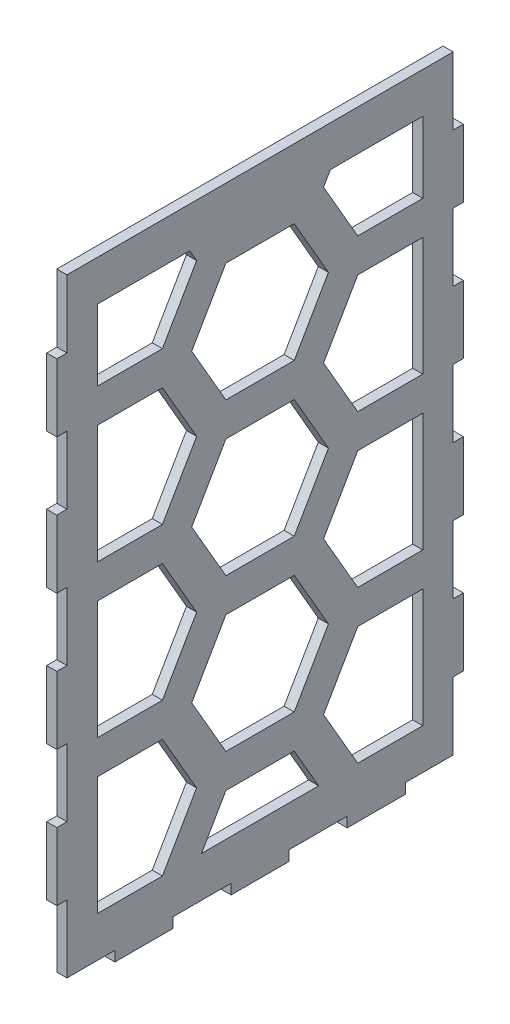
SolidWorks part; units mm, degrees
ref_plane "Front Plane" through (0, 0, 0) normal (0, 0, 1) x (1, 0, 0)
ref_plane "Top Plane" through (0, 0, 0) normal (0, 1, 0) x (1, 0, 0)
ref_plane "Right Plane" through (0, 0, 0) normal (1, 0, 0) x (0, 0, -1)
sketch "Sketch1" plane through (0, 0, 0) normal (1, 0, 0) x (0, 0, -1)
  line L1 (-57.0864, -90) -> (57.0864, -90)
  line L2 (-57.0864, -90) -> (-57.0864, 90)
  line L3 (-57.0864, 90) -> (57.0864, 90)
  line L4 (57.0864, -90) -> (57.0864, 90)
  line L5 (-57.0864, -90) -> (57.0864, 90) construction
  line L6 (-57.0864, 90) -> (57.0864, -90) construction
  point P0 (0, 0)
  dimension "D1" = 114.1727
  dimension "D2" = 180
extrude "Boss-Extrude1" add sketch "Sketch1" along normal blind 3
sketch "Sketch2" plane through (3, 0, 0) normal (1, 0, 0) x (0, 0, -1)
  line L0 (-57.0864, -90) -> (57.0864, -90) construction
  line L1 (-42.9188, -93) -> (-25.7513, -93)
  line L2 (-42.9188, -93) -> (-42.9188, -90)
  line L3 (-42.9188, -90) -> (-25.7513, -90)
  line L4 (-25.7513, -93) -> (-25.7513, -90)
  line L5 (-42.9188, -93) -> (-25.7513, -90) construction
  line L6 (-42.9188, -90) -> (-25.7513, -93) construction
  line L7 (-60.0864, -93) -> (-42.9188, -93) construction
  line L8 (-8.5838, -93) -> (8.5838, -93)
  line L9 (-8.5838, -93) -> (-8.5838, -90)
  line L10 (-8.5838, -90) -> (8.5838, -90)
  line L11 (8.5838, -93) -> (8.5838, -90)
  line L12 (-8.5838, -93) -> (8.5838, -90) construction
  line L13 (-8.5838, -90) -> (8.5838, -93) construction
  line L14 (25.7513, -93) -> (42.9188, -93)
  line L15 (25.7513, -93) -> (25.7513, -90)
  line L16 (25.7513, -90) -> (42.9188, -90)
  line L17 (42.9188, -93) -> (42.9188, -90)
  line L18 (25.7513, -93) -> (42.9188, -90) construction
  line L19 (25.7513, -90) -> (42.9188, -93) construction
  line L20 (-25.7513, -93) -> (-8.5838, -93) construction
  line L21 (8.5838, -93) -> (25.7513, -93) construction
  line L22 (42.9188, -93) -> (60.0864, -93) construction
  line L23 (-57.0864, 90) -> (-57.0864, -90) construction
  line L24 (57.0864, -90) -> (57.0864, 90) construction
  line L25 (60.0863, -70) -> (57.0864, -70)
  line L26 (60.0863, -70) -> (60.0864, -50)
  line L27 (60.0864, -50) -> (57.0864, -50)
  line L28 (57.0864, -70) -> (57.0864, -50)
  line L29 (60.0863, -70) -> (57.0864, -50) construction
  line L30 (60.0864, -50) -> (57.0864, -70) construction
  line L31 (60.0863, 90) -> (60.0863, 70) construction
  line L32 (60.0863, -30) -> (57.0864, -30)
  line L33 (60.0863, -30) -> (60.0863, -10)
  line L34 (60.0863, -10) -> (57.0864, -10)
  line L35 (57.0864, -30) -> (57.0864, -10)
  line L36 (60.0863, -30) -> (57.0864, -10) construction
  line L37 (60.0863, -10) -> (57.0864, -30) construction
  line L38 (60.0863, 10) -> (57.0864, 10)
  line L39 (60.0863, 10) -> (60.0863, 30)
  line L40 (60.0863, 30) -> (57.0864, 30)
  line L41 (57.0864, 10) -> (57.0864, 30)
  line L42 (60.0863, 10) -> (57.0864, 30) construction
  line L43 (60.0863, 30) -> (57.0864, 10) construction
  line L44 (60.0863, 50) -> (57.0864, 50)
  line L45 (60.0863, 50) -> (60.0863, 70)
  line L46 (60.0863, 70) -> (57.0864, 70)
  line L47 (57.0864, 50) -> (57.0864, 70)
  line L48 (60.0863, 50) -> (57.0864, 70) construction
  line L49 (60.0863, 70) -> (57.0864, 50) construction
  line L50 (60.0863, 50) -> (60.0863, 30) construction
  line L51 (60.0863, 10) -> (60.0863, -10) construction
  line L52 (60.0863, -30) -> (60.0864, -50) construction
  line L53 (60.0863, -70) -> (60.0863, -90) construction
  line L54 (57.0864, 90) -> (-57.0864, 90) construction
  line L55 (0, -895.4773) -> (0, 49104.5227) construction
  line L56 (-60.0864, -50) -> (-57.0864, -50)
  line L57 (-57.0864, -70) -> (-57.0864, -50)
  line L58 (-60.0863, -70) -> (-57.0864, -70)
  line L59 (-60.0863, -70) -> (-60.0864, -50)
  line L60 (-60.0863, -10) -> (-57.0864, -10)
  line L61 (-57.0864, -30) -> (-57.0864, -10)
  line L62 (-60.0863, -30) -> (-57.0864, -30)
  line L63 (-60.0863, -30) -> (-60.0863, -10)
  line L64 (-60.0863, 30) -> (-57.0864, 30)
  line L65 (-57.0864, 10) -> (-57.0864, 30)
  line L66 (-60.0863, 10) -> (-57.0864, 10)
  line L67 (-60.0863, 10) -> (-60.0863, 30)
  line L68 (-60.0863, 70) -> (-57.0864, 70)
  line L69 (-57.0864, 50) -> (-57.0864, 70)
  line L70 (-60.0863, 50) -> (-57.0864, 50)
  line L71 (-60.0863, 50) -> (-60.0863, 70)
  point P0 (-34.3351, -91.5)
  point P7 (0, -91.5)
  point P12 (34.3351, -91.5)
  point P24 (58.5864, -60)
  point P29 (58.5864, -20)
  point P34 (58.5863, 20)
  point P39 (58.5864, 60)
  dimension "D1" = 3
  dimension "D2" = 3
extrude "Boss-Extrude2" add sketch "Sketch2" against normal up to surface (3 mm away) up to face at (0, 0, 0)
sketch "Sketch3" plane through (0, 0, -3) normal (-1, 0, 0) x (0, 0, 1)
  line L0 (-142.7809, -20.5) -> (-162.9882, -20.5)
  line L1 (-142.7809, -65.5) -> (-162.9882, -65.5)
  line L2 (-162.9882, -65.5) -> (-173.0918, -83)
  line L3 (-173.0918, -83) -> (-162.9882, -100.5)
  line L4 (-162.9882, -100.5) -> (-142.7809, -100.5)
  line L5 (-142.7809, -100.5) -> (-132.6773, -83)
  line L6 (-132.6773, -83) -> (-142.7809, -65.5)
  line L13 (-162.9882, -20.5) -> (-173.0918, -38)
  line L14 (-134.1207, -105.5) -> (-124.0171, -123)
  line L15 (-124.0171, -123) -> (-103.8098, -123)
  line L16 (-103.8098, -123) -> (-93.7062, -105.5)
  line L17 (-93.7062, -105.5) -> (-103.8098, -88)
  line L18 (-103.8098, -88) -> (-124.0171, -88)
  line L19 (-124.0171, -88) -> (-134.1207, -105.5)
  line L20 (-173.0918, -38) -> (-162.9882, -55.5)
  line L21 (-162.9882, -55.5) -> (-142.7809, -55.5)
  line L22 (-142.7809, -55.5) -> (-132.6773, -38)
  line L23 (-132.6773, -38) -> (-142.7809, -20.5)
  line L24 (-134.1207, -60.5) -> (-124.0171, -78)
  line L25 (-124.0171, -78) -> (-103.8098, -78)
  line L26 (-103.8098, -78) -> (-93.7062, -60.5)
  line L27 (-93.7062, -60.5) -> (-103.8098, -43)
  line L28 (-103.8098, -43) -> (-124.0171, -43)
  line L29 (-124.0171, -43) -> (-134.1207, -60.5)
  line L30 (-142.7809, 24.5) -> (-162.9882, 24.5)
  line L31 (-162.9882, 24.5) -> (-173.0918, 7)
  line L32 (-173.0918, 7) -> (-162.9882, -10.5)
  line L33 (-162.9882, -10.5) -> (-142.7809, -10.5)
  line L34 (-142.7809, -10.5) -> (-132.6773, 7)
  line L35 (-132.6773, 7) -> (-142.7809, 24.5)
  line L36 (-134.1207, -15.5) -> (-124.0171, -33)
  line L37 (-124.0171, -33) -> (-103.8098, -33)
  line L38 (-103.8098, -33) -> (-93.7062, -15.5)
  line L39 (-93.7062, -15.5) -> (-103.8098, 2)
  line L40 (-103.8098, 2) -> (-124.0171, 2)
  line L41 (-124.0171, 2) -> (-134.1207, -15.5)
  line L42 (-142.7809, 69.5) -> (-162.9882, 69.5)
  line L43 (-162.9882, 69.5) -> (-173.0918, 52)
  line L44 (-173.0918, 52) -> (-162.9882, 34.5)
  line L45 (-162.9882, 34.5) -> (-142.7809, 34.5)
  line L46 (-142.7809, 34.5) -> (-132.6773, 52)
  line L47 (-132.6773, 52) -> (-142.7809, 69.5)
  line L48 (-134.1207, 29.5) -> (-124.0171, 12)
  line L49 (-124.0171, 12) -> (-103.8098, 12)
  line L50 (-103.8098, 12) -> (-93.7062, 29.5)
  line L51 (-93.7062, 29.5) -> (-103.8098, 47)
  line L52 (-103.8098, 47) -> (-124.0171, 47)
  line L53 (-124.0171, 47) -> (-134.1207, 29.5)
  line L54 (-142.7809, 114.5) -> (-162.9882, 114.5)
  line L55 (-162.9882, 114.5) -> (-173.0918, 97)
  line L56 (-173.0918, 97) -> (-162.9882, 79.5)
  line L57 (-162.9882, 79.5) -> (-142.7809, 79.5)
  line L58 (-142.7809, 79.5) -> (-132.6773, 97)
  line L59 (-132.6773, 97) -> (-142.7809, 114.5)
  line L60 (-134.1207, 74.5) -> (-124.0171, 57)
  line L61 (-124.0171, 57) -> (-103.8098, 57)
  line L62 (-103.8098, 57) -> (-93.7062, 74.5)
  line L63 (-93.7062, 74.5) -> (-103.8098, 92)
  line L64 (-103.8098, 92) -> (-124.0171, 92)
  line L65 (-124.0171, 92) -> (-134.1207, 74.5)
  line L66 (-142.7809, 159.5) -> (-162.9882, 159.5)
  line L67 (-162.9882, 159.5) -> (-173.0918, 142)
  line L68 (-173.0918, 142) -> (-162.9882, 124.5)
  line L69 (-162.9882, 124.5) -> (-142.7809, 124.5)
  line L70 (-142.7809, 124.5) -> (-132.6773, 142)
  line L71 (-132.6773, 142) -> (-142.7809, 159.5)
  line L72 (-134.1207, 119.5) -> (-124.0171, 102)
  line L73 (-124.0171, 102) -> (-103.8098, 102)
  line L74 (-103.8098, 102) -> (-93.7062, 119.5)
  line L75 (-93.7062, 119.5) -> (-103.8098, 137)
  line L76 (-103.8098, 137) -> (-124.0171, 137)
  line L77 (-124.0171, 137) -> (-134.1207, 119.5)
  line L102 (-142.7809, -65.5) -> (-142.7809, -20.5) construction
  line L103 (-124.0171, -88) -> (-124.0171, -78) construction
  line L104 (-137.7291, -74.25) -> (-129.0689, -69.25) construction
  line L105 (-56.1784, 119.5) -> (-46.0748, 102)
  line L106 (-46.0748, 102) -> (-25.8675, 102)
  line L107 (-25.8675, 102) -> (-15.7639, 119.5)
  line L108 (-15.7639, 119.5) -> (-25.8675, 137)
  line L109 (-25.8675, 137) -> (-46.0748, 137)
  line L110 (-46.0748, 137) -> (-56.1784, 119.5)
  line L111 (-64.8387, 159.5) -> (-85.0459, 159.5)
  line L112 (-85.0459, 159.5) -> (-95.1495, 142)
  line L113 (-95.1495, 142) -> (-85.0459, 124.5)
  line L114 (-85.0459, 124.5) -> (-64.8387, 124.5)
  line L115 (-64.8387, 124.5) -> (-54.735, 142)
  line L116 (-54.735, 142) -> (-64.8387, 159.5)
  line L117 (-64.8387, 114.5) -> (-85.0459, 114.5)
  line L118 (-85.0459, 114.5) -> (-95.1495, 97)
  line L119 (-95.1495, 97) -> (-85.0459, 79.5)
  line L120 (-85.0459, 79.5) -> (-64.8387, 79.5)
  line L121 (-64.8387, 79.5) -> (-54.735, 97)
  line L122 (-54.735, 97) -> (-64.8387, 114.5)
  line L123 (-64.8387, 69.5) -> (-85.0459, 69.5)
  line L124 (-85.0459, 69.5) -> (-95.1495, 52)
  line L125 (-95.1495, 52) -> (-85.0459, 34.5)
  line L126 (-85.0459, 34.5) -> (-64.8387, 34.5)
  line L127 (-64.8387, 34.5) -> (-54.735, 52)
  line L128 (-54.735, 52) -> (-64.8387, 69.5)
  line L129 (-64.8387, 24.5) -> (-85.0459, 24.5)
  line L130 (-85.0459, 24.5) -> (-95.1495, 7)
  line L131 (-95.1495, 7) -> (-85.0459, -10.5)
  line L132 (-85.0459, -10.5) -> (-64.8387, -10.5)
  line L133 (-64.8387, -10.5) -> (-54.735, 7)
  line L134 (-54.735, 7) -> (-64.8387, 24.5)
  line L135 (-56.1784, -15.5) -> (-46.0748, -33)
  line L136 (-46.0748, -33) -> (-25.8675, -33)
  line L137 (-25.8675, -33) -> (-15.7639, -15.5)
  line L138 (-15.7639, -15.5) -> (-25.8675, 2)
  line L139 (-25.8675, 2) -> (-46.0748, 2)
  line L140 (-46.0748, 2) -> (-56.1784, -15.5)
  line L141 (-64.8387, -20.5) -> (-85.0459, -20.5)
  line L142 (-85.0459, -20.5) -> (-95.1495, -38)
  line L143 (-95.1495, -38) -> (-85.0459, -55.5)
  line L144 (-85.0459, -55.5) -> (-64.8387, -55.5)
  line L145 (-64.8387, -55.5) -> (-54.735, -38)
  line L146 (-54.735, -38) -> (-64.8387, -20.5)
  line L147 (-56.1784, -60.5) -> (-46.0748, -78)
  line L148 (-46.0748, -78) -> (-25.8675, -78)
  line L149 (-25.8675, -78) -> (-15.7639, -60.5)
  line L150 (-15.7639, -60.5) -> (-25.8675, -43)
  line L151 (-25.8675, -43) -> (-46.0748, -43)
  line L152 (-46.0748, -43) -> (-56.1784, -60.5)
  line L153 (-64.8387, -65.5) -> (-85.0459, -65.5)
  line L154 (-85.0459, -65.5) -> (-95.1495, -83)
  line L155 (-95.1495, -83) -> (-85.0459, -100.5)
  line L156 (-85.0459, -100.5) -> (-64.8387, -100.5)
  line L157 (-64.8387, -100.5) -> (-54.735, -83)
  line L158 (-54.735, -83) -> (-64.8387, -65.5)
  line L159 (-56.1784, -105.5) -> (-46.0748, -123)
  line L160 (-46.0748, -123) -> (-25.8675, -123)
  line L161 (-25.8675, -123) -> (-15.7639, -105.5)
  line L162 (-15.7639, -105.5) -> (-25.8675, -88)
  line L163 (-25.8675, -88) -> (-46.0748, -88)
  line L164 (-46.0748, -88) -> (-56.1784, -105.5)
  line L165 (-56.1784, 29.5) -> (-46.0748, 12)
  line L166 (-46.0748, 12) -> (-25.8675, 12)
  line L167 (-25.8675, 12) -> (-15.7639, 29.5)
  line L168 (-15.7639, 29.5) -> (-25.8675, 47)
  line L169 (-25.8675, 47) -> (-46.0748, 47)
  line L170 (-46.0748, 47) -> (-56.1784, 29.5)
  line L171 (-56.1784, 74.5) -> (-46.0748, 57)
  line L172 (-46.0748, 57) -> (-25.8675, 57)
  line L173 (-25.8675, 57) -> (-15.7639, 74.5)
  line L174 (-15.7639, 74.5) -> (-25.8675, 92)
  line L175 (-25.8675, 92) -> (-46.0748, 92)
  line L176 (-46.0748, 92) -> (-56.1784, 74.5)
  line L177 (21.7639, 119.5) -> (31.8675, 102)
  line L178 (31.8675, 102) -> (52.0748, 102)
  line L179 (52.0748, 102) -> (62.1784, 119.5)
  line L180 (62.1784, 119.5) -> (52.0748, 137)
  line L181 (52.0748, 137) -> (31.8675, 137)
  line L182 (31.8675, 137) -> (21.7639, 119.5)
  line L183 (13.1036, 159.5) -> (-7.1036, 159.5)
  line L184 (-7.1036, 159.5) -> (-17.2073, 142)
  line L185 (-17.2073, 142) -> (-7.1036, 124.5)
  line L186 (-7.1036, 124.5) -> (13.1036, 124.5)
  line L187 (13.1036, 124.5) -> (23.2073, 142)
  line L188 (23.2073, 142) -> (13.1036, 159.5)
  line L189 (13.1036, 114.5) -> (-7.1036, 114.5)
  line L190 (-7.1036, 114.5) -> (-17.2073, 97)
  line L191 (-17.2073, 97) -> (-7.1036, 79.5)
  line L192 (-7.1036, 79.5) -> (13.1036, 79.5)
  line L193 (13.1036, 79.5) -> (23.2073, 97)
  line L194 (23.2073, 97) -> (13.1036, 114.5)
  line L195 (13.1036, 69.5) -> (-7.1036, 69.5)
  line L196 (-7.1036, 69.5) -> (-17.2073, 52)
  line L197 (-17.2073, 52) -> (-7.1036, 34.5)
  line L198 (-7.1036, 34.5) -> (13.1036, 34.5)
  line L199 (13.1036, 34.5) -> (23.2073, 52)
  line L200 (23.2073, 52) -> (13.1036, 69.5)
  line L201 (13.1036, 24.5) -> (-7.1036, 24.5)
  line L202 (-7.1036, 24.5) -> (-17.2073, 7)
  line L203 (-17.2073, 7) -> (-7.1036, -10.5)
  line L204 (-7.1036, -10.5) -> (13.1036, -10.5)
  line L205 (13.1036, -10.5) -> (23.2073, 7)
  line L206 (23.2073, 7) -> (13.1036, 24.5)
  line L207 (21.7639, -15.5) -> (31.8675, -33)
  line L208 (31.8675, -33) -> (52.0748, -33)
  line L209 (52.0748, -33) -> (62.1784, -15.5)
  line L210 (62.1784, -15.5) -> (52.0748, 2)
  line L211 (52.0748, 2) -> (31.8675, 2)
  line L212 (31.8675, 2) -> (21.7639, -15.5)
  line L213 (13.1036, -20.5) -> (-7.1036, -20.5)
  line L214 (-7.1036, -20.5) -> (-17.2073, -38)
  line L215 (-17.2073, -38) -> (-7.1036, -55.5)
  line L216 (-7.1036, -55.5) -> (13.1036, -55.5)
  line L217 (13.1036, -55.5) -> (23.2073, -38)
  line L218 (23.2073, -38) -> (13.1036, -20.5)
  line L219 (21.7639, -60.5) -> (31.8675, -78)
  line L220 (31.8675, -78) -> (52.0748, -78)
  line L221 (52.0748, -78) -> (62.1784, -60.5)
  line L222 (62.1784, -60.5) -> (52.0748, -43)
  line L223 (52.0748, -43) -> (31.8675, -43)
  line L224 (31.8675, -43) -> (21.7639, -60.5)
  line L225 (13.1036, -65.5) -> (-7.1036, -65.5)
  line L226 (-7.1036, -65.5) -> (-17.2073, -83)
  line L227 (-17.2073, -83) -> (-7.1036, -100.5)
  line L228 (-7.1036, -100.5) -> (13.1036, -100.5)
  line L229 (13.1036, -100.5) -> (23.2073, -83)
  line L230 (23.2073, -83) -> (13.1036, -65.5)
  line L231 (21.7639, -105.5) -> (31.8675, -123)
  line L232 (31.8675, -123) -> (52.0748, -123)
  line L233 (52.0748, -123) -> (62.1784, -105.5)
  line L234 (62.1784, -105.5) -> (52.0748, -88)
  line L235 (52.0748, -88) -> (31.8675, -88)
  line L236 (31.8675, -88) -> (21.7639, -105.5)
  line L237 (21.7639, 29.5) -> (31.8675, 12)
  line L238 (31.8675, 12) -> (52.0748, 12)
  line L239 (52.0748, 12) -> (62.1784, 29.5)
  line L240 (62.1784, 29.5) -> (52.0748, 47)
  line L241 (52.0748, 47) -> (31.8675, 47)
  line L242 (31.8675, 47) -> (21.7639, 29.5)
  line L243 (21.7639, 74.5) -> (31.8675, 57)
  line L244 (31.8675, 57) -> (52.0748, 57)
  line L245 (52.0748, 57) -> (62.1784, 74.5)
  line L246 (62.1784, 74.5) -> (52.0748, 92)
  line L247 (52.0748, 92) -> (31.8675, 92)
  line L248 (31.8675, 92) -> (21.7639, 74.5)
  line L249 (99.7062, 119.5) -> (109.8098, 102)
  line L250 (109.8098, 102) -> (130.0171, 102)
  line L251 (130.0171, 102) -> (140.1207, 119.5)
  line L252 (140.1207, 119.5) -> (130.0171, 137)
  line L253 (130.0171, 137) -> (109.8098, 137)
  line L254 (109.8098, 137) -> (99.7062, 119.5)
  line L255 (91.0459, 159.5) -> (70.8387, 159.5)
  line L256 (70.8387, 159.5) -> (60.735, 142)
  line L257 (60.735, 142) -> (70.8387, 124.5)
  line L258 (70.8387, 124.5) -> (91.0459, 124.5)
  line L259 (91.0459, 124.5) -> (101.1495, 142)
  line L260 (101.1495, 142) -> (91.0459, 159.5)
  line L261 (91.0459, 114.5) -> (70.8387, 114.5)
  line L262 (70.8387, 114.5) -> (60.735, 97)
  line L263 (60.735, 97) -> (70.8387, 79.5)
  line L264 (70.8387, 79.5) -> (91.0459, 79.5)
  line L265 (91.0459, 79.5) -> (101.1495, 97)
  line L266 (101.1495, 97) -> (91.0459, 114.5)
  line L267 (91.0459, 69.5) -> (70.8387, 69.5)
  line L268 (70.8387, 69.5) -> (60.735, 52)
  line L269 (60.735, 52) -> (70.8387, 34.5)
  line L270 (70.8387, 34.5) -> (91.0459, 34.5)
  line L271 (91.0459, 34.5) -> (101.1495, 52)
  line L272 (101.1495, 52) -> (91.0459, 69.5)
  line L273 (91.0459, 24.5) -> (70.8387, 24.5)
  line L274 (70.8387, 24.5) -> (60.735, 7)
  line L275 (60.735, 7) -> (70.8387, -10.5)
  line L276 (70.8387, -10.5) -> (91.0459, -10.5)
  line L277 (91.0459, -10.5) -> (101.1495, 7)
  line L278 (101.1495, 7) -> (91.0459, 24.5)
  line L279 (99.7062, -15.5) -> (109.8098, -33)
  line L280 (109.8098, -33) -> (130.0171, -33)
  line L281 (130.0171, -33) -> (140.1207, -15.5)
  line L282 (140.1207, -15.5) -> (130.0171, 2)
  line L283 (130.0171, 2) -> (109.8098, 2)
  line L284 (109.8098, 2) -> (99.7062, -15.5)
  line L285 (91.0459, -20.5) -> (70.8387, -20.5)
  line L286 (70.8387, -20.5) -> (60.735, -38)
  line L287 (60.735, -38) -> (70.8387, -55.5)
  line L288 (70.8387, -55.5) -> (91.0459, -55.5)
  line L289 (91.0459, -55.5) -> (101.1495, -38)
  line L290 (101.1495, -38) -> (91.0459, -20.5)
  line L291 (99.7062, -60.5) -> (109.8098, -78)
  line L292 (109.8098, -78) -> (130.0171, -78)
  line L293 (130.0171, -78) -> (140.1207, -60.5)
  line L294 (140.1207, -60.5) -> (130.0171, -43)
  line L295 (130.0171, -43) -> (109.8098, -43)
  line L296 (109.8098, -43) -> (99.7062, -60.5)
  line L297 (91.0459, -65.5) -> (70.8387, -65.5)
  line L298 (70.8387, -65.5) -> (60.735, -83)
  line L299 (60.735, -83) -> (70.8387, -100.5)
  line L300 (70.8387, -100.5) -> (91.0459, -100.5)
  line L301 (91.0459, -100.5) -> (101.1495, -83)
  line L302 (101.1495, -83) -> (91.0459, -65.5)
  line L303 (99.7062, -105.5) -> (109.8098, -123)
  line L304 (109.8098, -123) -> (130.0171, -123)
  line L305 (130.0171, -123) -> (140.1207, -105.5)
  line L306 (140.1207, -105.5) -> (130.0171, -88)
  line L307 (130.0171, -88) -> (109.8098, -88)
  line L308 (109.8098, -88) -> (99.7062, -105.5)
  line L309 (99.7062, 29.5) -> (109.8098, 12)
  line L310 (109.8098, 12) -> (130.0171, 12)
  line L311 (130.0171, 12) -> (140.1207, 29.5)
  line L312 (140.1207, 29.5) -> (130.0171, 47)
  line L313 (130.0171, 47) -> (109.8098, 47)
  line L314 (109.8098, 47) -> (99.7062, 29.5)
  line L315 (99.7062, 74.5) -> (109.8098, 57)
  line L316 (109.8098, 57) -> (130.0171, 57)
  line L317 (130.0171, 57) -> (140.1207, 74.5)
  line L318 (140.1207, 74.5) -> (130.0171, 92)
  line L319 (130.0171, 92) -> (109.8098, 92)
  line L320 (109.8098, 92) -> (99.7062, 74.5)
  line L321 (-134.1207, 119.5) -> (-56.1784, 119.5) construction
  line L322 (-90.0977, -74.25) -> (-98.758, -69.25) construction
  line L324 (-45.0863, -78) -> (51.0863, -78)
  line L325 (-45.0863, -78) -> (-45.0863, 78)
  line L326 (-45.0863, 78) -> (51.0863, 78)
  line L327 (51.0863, -78) -> (51.0863, 78)
  line L328 (-45.0863, -78) -> (51.0863, 78) construction
  line L329 (-45.0863, 78) -> (51.0863, -78) construction
  line L331 (-103.8098, -43) -> (-45.0863, -43) construction
  line L332 (109.8098, -43) -> (51.0863, -43) construction
  line L333 (-54.0864, 90) -> (60.0864, 90) construction
  line L334 (63.0863, 30) -> (63.0863, 10) construction
  circle A0 centre (-152.8846, -83) radius 17.5 construction
  circle A1 centre (-113.9134, -105.5) radius 17.5 construction
  point P10 (-124.0171, -83)
  point P301 (3, 0)
  point P307 (3, 24.5)
  point P308 (-3.0902, 41.9635)
  point P309 (-0.3483, 0)
  point P310 (0, 0)
  point P311 (0, 0)
  dimension "D3" = 35
  dimension "D2" = 45
  dimension "D5" = 12
  dimension "D6" = 12
  dimension "D1" = 6
  dimension "D4" = 4
extrude "Cut-Extrude1" cut sketch "Sketch3" against normal blind 10 contours L148 L325 L151 L150 L149 | L324 L226 L225 L230 | L327 L220 L219 L224 L223 | L218 L217 L216 L215 L214 L213 | L136 L325 L139 L138 L137 | L206 L205 L204 L203 L202 L201 | L327 L208 L207 L212 L211 | L327 L238 L237 L242 L241 | L166 L325 L169 L168 L167 | L200 L199 L198 L197 L196 L195 | L325 L326 L174 L173 L172 | L327 L244 L243 L248 L326
